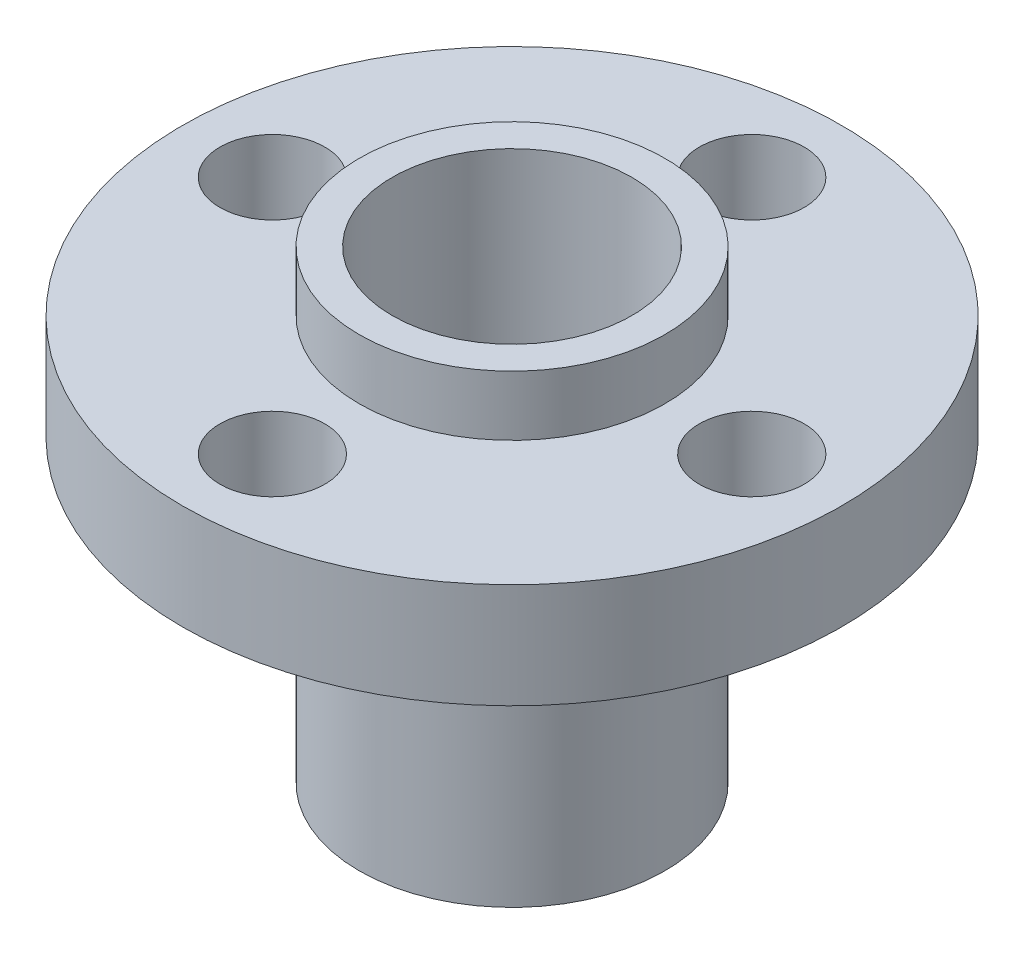
SolidWorks part; units mm, degrees
ref_plane "前视基准面" through (0, 0, 0) normal (0, 0, 1) x (1, 0, 0)
ref_plane "上视基准面" through (0, 0, 0) normal (0, 1, 0) x (1, 0, 0)
ref_plane "右视基准面" through (0, 0, 0) normal (1, 0, 0) x (0, 0, -1)
sketch "草图1" plane through (0, 0, 0) normal (0, 1, 0) x (1, 0, 0)
  circle A0 centre (0, 0) radius 5.1
  dimension "D1" = 10.2
extrude "凸台-拉伸1" add sketch "草图1" along normal blind 10
sketch "草图2" plane through (0, 10, 0) normal (0, 1, 0) x (1, 0, 0)
  circle A0 centre (0, 0) radius 11
  dimension "D1" = 22
extrude "凸台-拉伸2" add sketch "草图2" along normal blind 3.5
sketch "草图3" plane through (0, 13.5, 0) normal (0, 1, 0) x (1, 0, 0)
  circle A0 centre (0, 0) radius 5.1
  dimension "D1" = 10.2
extrude "凸台-拉伸3" add sketch "草图3" along normal blind 2
sketch "草图4" plane through (0, 15.5, 0) normal (0, 1, 0) x (1, 0, 0)
  line L0 (0, 0) -> (10.4682, 0) construction
  line L1 (0, 0) -> (0, 3.5404) construction
  circle A0 centre (0, 0) radius 4
  circle A1 centre (-8, 0) radius 1.75
  circle A2 centre (0, -8) radius 1.75
  circle A3 centre (8, 0) radius 1.75
  circle A4 centre (0, 8) radius 1.75
  circle A5 centre (0, 0) radius 8 construction
  dimension "D1" = 3.5
  dimension "D2" = 3.5
  dimension "D3" = 3.5
  dimension "D4" = 3.5
  dimension "D5" = 8
  dimension "D6" = 16
extrude "切除-拉伸1" cut sketch "草图4" against normal through all
